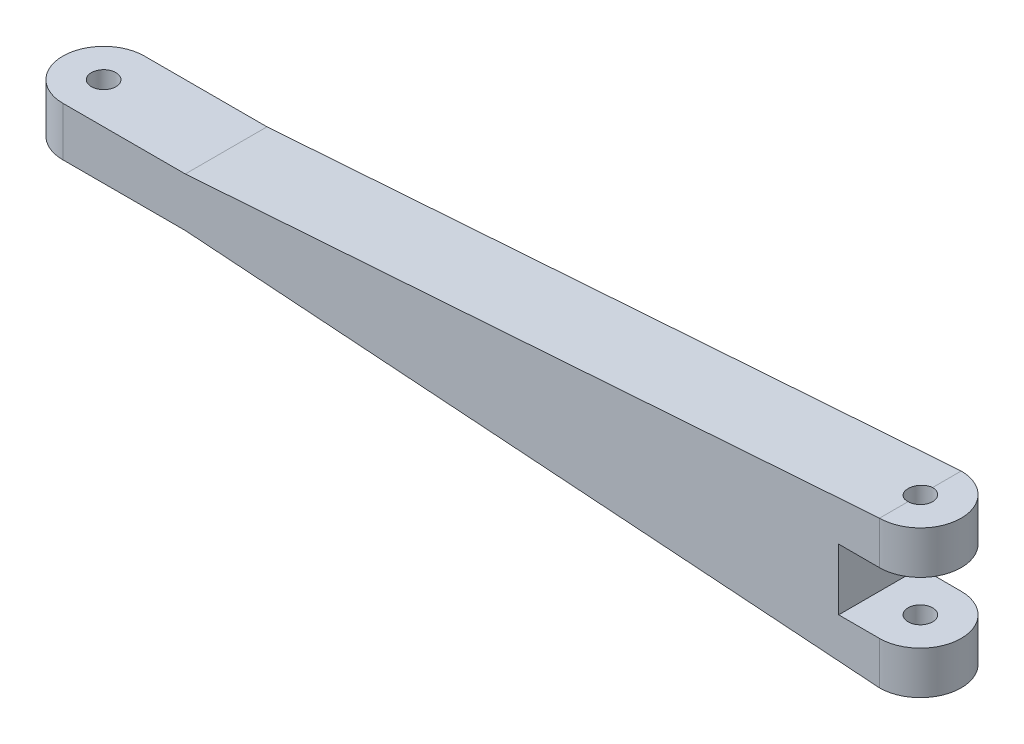
SolidWorks part; units mm, degrees
ref_plane "Front Plane" through (0, 0, 0) normal (0, 0, 1) x (1, 0, 0)
ref_plane "Top Plane" through (0, 0, 0) normal (0, 1, 0) x (1, 0, 0)
ref_plane "Right Plane" through (0, 0, 0) normal (1, 0, 0) x (0, 0, -1)
sketch "Sketch2" plane through (0, 0, 0) normal (0, 1, 0) x (1, 0, 0)
  line L0 (-50, 2.5) -> (0, 2.5)
  line L1 (-50, -2.5) -> (0, -2.5)
  arc A0 (-50, 2.5) -> (-50, -2.5) centre (-50, 0) ccw
  arc A1 (0, -2.5) -> (0, 2.5) centre (0, 0) ccw
  dimension "D2" = 2.5
  dimension "D1" = 50
extrude "Boss-Extrude2" add sketch "Sketch2" along normal mid plane 9 contours L0 A1 L1 A0
sketch "Sketch3" plane through (0, 0, 0) normal (0, 0, 1) x (1, 0, 0)
  line L0 (-52.5, -1.5) -> (-42.5, -1.5)
  line L1 (-52.5, 4.5) -> (-52.5, -4.5) construction
  line L2 (-52.5, 1.5) -> (-42.5, 1.5)
  line L3 (-42.5, 1.5) -> (0, 4.5)
  line L4 (0, 4.5) -> (-52.5, 4.5)
  line L5 (-52.5, 4.5) -> (-52.5, 1.5)
  line L6 (-52.5, -1.5) -> (-52.5, -4.5)
  line L7 (-52.5, -4.5) -> (0, -4.5)
  line L8 (-42.5, -1.5) -> (0, -4.5)
  dimension "D1" = 3
  dimension "D2" = 3
  dimension "D3" = 10
extrude "Cut-Extrude3" cut sketch "Sketch3" against normal through all and the other way through all
sketch "Sketch4" plane through (0, 0, 0) normal (0, 1, 0) x (1, 0, 0)
  circle A0 centre (0, 0) radius 2.5
  dimension "D1" = 5
extrude "Cut-Extrude4" cut sketch "Sketch4" against normal mid plane 3.75
sketch "Sketch6" plane through (0, 0, 0) normal (0, 1, 0) x (1, 0, 0)
  circle A0 centre (-50, 0) radius 0.75
  circle A1 centre (0, 0) radius 0.75
  dimension "D1" = 1.5
extrude "Cut-Extrude6" cut sketch "Sketch6" against normal through all and the other way through all contours A1 | A0
sketch "Sketch8" plane through (0, 0, 0) normal (0, 0, 1) x (1, 0, 0)
  line L0 (2.5, 1.875) -> (-2.5, 1.875)
  line L1 (2.5, -1.875) -> (-2.5, -1.875)
  line L2 (-2.5, -1.875) -> (-2.5, 1.875)
  line L3 (2.5, 1.875) -> (2.5, -1.875)
  dimension "D1" = 5
extrude "Cut-Extrude10" cut sketch "Sketch8" against normal mid plane 40
equation "\"length\"= 50mm"
equation "\"radius\"= 5mm"
equation "\"depth\"= 9mm"
equation "\"D1@Sketch2\"= \"length\""
equation "\"D2@Sketch2\"=\"radius\"/2"
equation "\"D1@Boss-Extrude2\"= \"depth\""
equation "\"D1@Sketch3\"=\"depth\"/3"
equation "\"D2@Sketch3\"= \"depth\"/3"
equation "\"D1@Sketch4\"=\"radius\""
equation "\"D1@Cut-Extrude4\"=\"depth\"/3 + \"tolerance\""
equation "\"D3@Sketch3\"=\"radius\"*2"
equation "\"inner diamer\"= 3mm"
equation "\"D1@Sketch6\"=\"inner diamer\"/2"
equation "\"D1@Sketch8\" = \"radius\""
equation "\"tolerance\"= 0.75mm"
